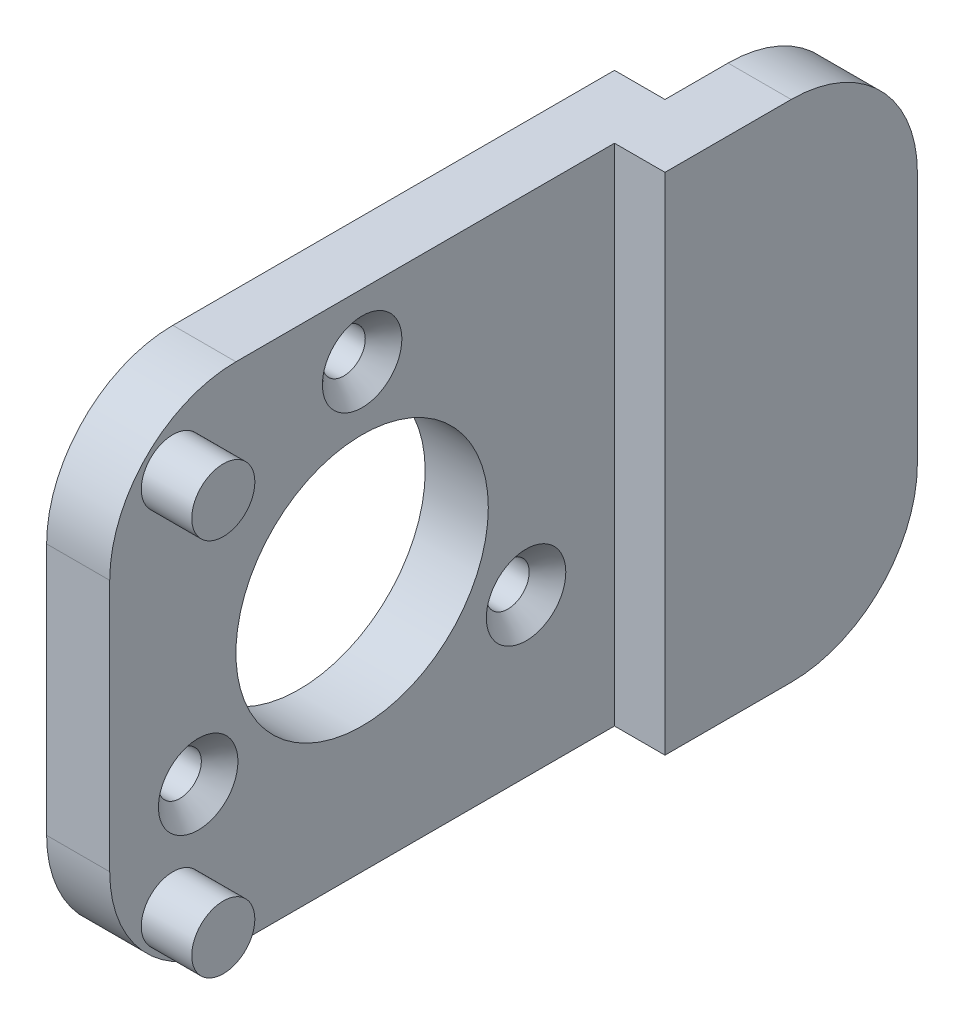
SolidWorks part; units mm, degrees
ref_plane "Ön Düzlem" through (0, 0, 0) normal (0, 0, 1) x (1, 0, 0)
ref_plane "Üst Düzlem" through (0, 0, 0) normal (0, 1, 0) x (1, 0, 0)
ref_plane "Sağ Düzlem" through (0, 0, 0) normal (1, 0, 0) x (0, 0, -1)
sketch "Sketch1" plane through (0, 0, 0) normal (1, 0, 0) x (0, 0, -1)
  line L0 (10, 20) -> (20, 20)
  line L1 (-10, 20) -> (10, 20)
  line L2 (-20, 10) -> (-20, -10)
  line L3 (-10, -20) -> (10, -20)
  line L4 (20, 10) -> (20, -10)
  line L5 (-20, 20) -> (20, -20) construction
  line L6 (-20, -20) -> (20, 20) construction
  line L7 (20, 20) -> (20, 10)
  line L8 (20, -10) -> (20, -20)
  line L9 (20, -20) -> (10, -20)
  circle A0 centre (0, 0) radius 10
  arc A1 (-20, -10) -> (-10, -20) centre (-10, -10) ccw
  arc A4 (-10, 20) -> (-20, 10) centre (-10, 10) ccw
  dimension "D1" = 40
  dimension "D3" = 10
  dimension "D2" = 40
extrude "Boss-Extrude1" add sketch "Sketch1" along normal blind 5
hole_wizard "CSK for M3 Flat Head Machine Screw1" positions "Sketch3" profile "Sketch2" countersink size "M3" standard "ANSI Metric" end condition through all
sketch "Sketch3" plane through (5, 0, 0) normal (1, 0, 0) x (0, 0, -1)
  point P0 (0, 15)
  point P3 (12.9904, -7.5)
  point P6 (-12.9904, -7.5)
sketch "Sketch2" plane through (5, 15, 0) normal (0, 1, 0) x (0, 0, -1)
  line L0 (0, 0) -> (0, 5)
  line L1 (0, 5) -> (1.7, 5)
  line L2 (1.7, 5) -> (1.7, 1.45)
  line L3 (1.7, 1.45) -> (3.15, 0)
  line L5 (3.15, 0) -> (0, 0)
  line L6 (-1.7, 1.45) -> (-3.15, 0) construction
  line L11 (0, -6.35) -> (0, 107.95) construction
  dimension "Thru Hole Dia." = 3.4
  dimension "Thru Hole Depth" = 5
  dimension "Near C'Sink Dia." = 6.3
  dimension "Near C'Sink Angle" = 90
sketch "Sketch4" plane through (0, 0, 0) normal (-1, 0, 0) x (0, 0, 1)
  line L1 (-20, -20) -> (-25, -20)
  line L2 (-20, -20) -> (-20, 20)
  line L3 (-20, 20) -> (-25, 20)
  line L4 (-25, -20) -> (-25, 20)
  dimension "D1" = 40
  dimension "D2" = 5
extrude "Boss-Extrude2" add sketch "Sketch4" against normal blind 9
sketch "Sketch5" plane through (0, 0, -25) normal (0, 0, -1) x (-1, 0, 0)
  line L0 (-9, 20) -> (0, 20) construction
  line L1 (-9, -20) -> (-4, -20)
  line L2 (-9, -20) -> (-9, 20)
  line L3 (-9, 20) -> (-4, 20)
  line L4 (-4, -20) -> (-4, 20)
  dimension "D1" = 5
extrude "Boss-Extrude3" add sketch "Sketch5" along normal blind 15
fillet "Fillet2" radius 10 2 edges at (6.5, 20, -40) (6.5, -20, -40)
sketch "Sketch6" plane through (5, 0, 0) normal (1, 0, 0) x (0, 0, -1)
  line L0 (-10, -20) -> (20, -20) construction
  line L2 (-20, 10) -> (-20, -10) construction
  line L3 (-20, 10) -> (-20, -10) construction
  line L4 (20, 20) -> (-10, 20) construction
  circle A0 centre (-15, -15) radius 2.5
  circle A1 centre (-15, 15) radius 2.5
  dimension "D1" = 5
  dimension "D2" = 5
  dimension "D3" = 5
  dimension "D4" = 5
extrude "Boss-Extrude4" add sketch "Sketch6" along normal blind 4
